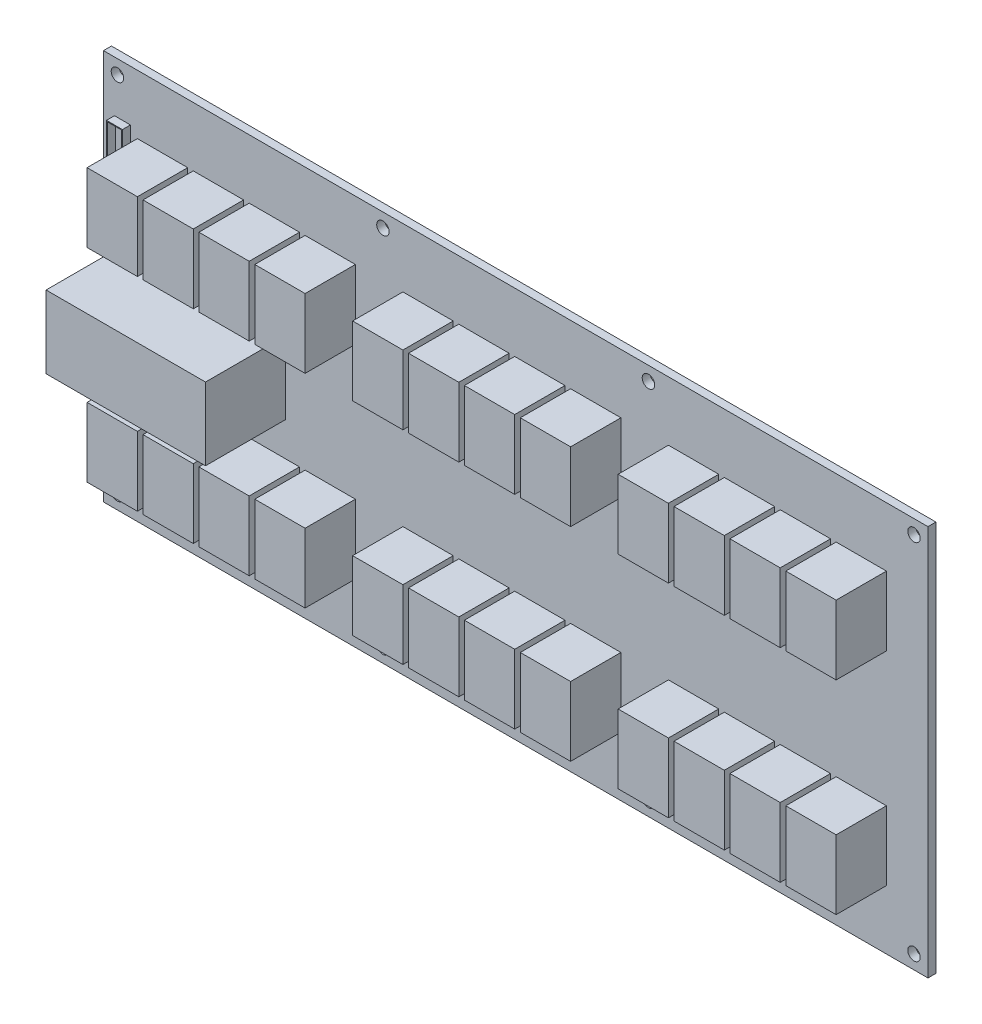
SolidWorks part; units mm, degrees
ref_plane "Front Plane" through (0, 0, 0) normal (0, 0, 1) x (1, 0, 0)
ref_plane "Top Plane" through (0, 0, 0) normal (0, 1, 0) x (1, 0, 0)
ref_plane "Right Plane" through (0, 0, 0) normal (1, 0, 0) x (0, 0, -1)
sketch "Sketch1" plane through (0, 0, 0) normal (0, 0, 1) x (1, 0, 0)
  line L1 (0, 0) -> (262.255, 0)
  line L2 (0, 0) -> (0, 124.333)
  line L3 (0, 124.333) -> (262.255, 124.333)
  line L4 (262.255, 0) -> (262.255, 124.333)
  dimension "D1" = 262.255
  dimension "D2" = 124.333
extrude "Boss-Extrude1" add sketch "Sketch1" along normal blind 2.54
hole_wizard "5/32 (0.15625) Diameter Hole1" positions "Sketch4" profile "Sketch3" hole size "5/32" standard "ANSI Inch" end condition through all
sketch "Sketch4" plane through (0, 0, 2.54) normal (0, 0, 1) x (1, 0, 0)
  line L0 (0, 124.333) -> (0, 0) construction
  line L1 (262.255, 124.333) -> (0, 124.333) construction
  line L2 (0, 0) -> (262.255, 0) construction
  point P0 (4.445, 119.888)
  point P2 (88.9, 119.888)
  point P4 (173.355, 119.888)
  point P6 (257.81, 119.888)
  point P8 (4.445, 4.445)
  point P10 (88.9, 4.445)
  point P12 (173.355, 4.445)
  point P14 (257.81, 4.445)
  dimension "D1" = 4.445
  dimension "D2" = 4.445
  dimension "D3" = 4.445
  dimension "D4" = 84.455
  dimension "D5" = 84.455
  dimension "D6" = 84.455
sketch "Sketch3" plane through (4.445, 119.888, 2.54) normal (1, 0, 0) x (0, -1, 0)
  line L0 (0, 0) -> (0, 2.54)
  line L1 (0, 2.54) -> (1.9844, 2.54)
  line L2 (1.9844, 2.54) -> (1.9844, 0)
  line L5 (1.9844, 0) -> (0, 0)
  line L11 (0, -6.35) -> (0, 107.95) construction
  dimension "Thru Hole Dia." = 3.9688
  dimension "Thru Hole Depth" = 2.54
sketch "Sketch12" plane through (0, 0, 2.54) normal (0, 0, 1) x (1, 0, 0)
  line L1 (3.5048, 108.1512) -> (8.5848, 108.1512)
  line L2 (3.5048, 108.1512) -> (3.5048, 81.2272)
  line L3 (3.5048, 81.2272) -> (8.5848, 81.2272)
  line L4 (8.5848, 108.1512) -> (8.5848, 81.2272)
  line L5 (3.8802, 107.8854) -> (8.2478, 107.8854)
  line L6 (3.8802, 107.8854) -> (3.8802, 81.6126)
  line L7 (3.8802, 81.6126) -> (8.2478, 81.6126)
  line L8 (8.2478, 107.8854) -> (8.2478, 81.6126)
extrude "Boss-Extrude2" add sketch "Sketch12" along normal blind 2.54
sketch "Sketch13" plane through (0, 0, 2.54) normal (0, 0, 1) x (1, 0, 0)
  line L1 (7.1463, 74.6686) -> (57.8568, 74.6686)
  line L2 (7.1463, 74.6686) -> (7.1463, 51.5898)
  line L3 (7.1463, 51.5898) -> (57.8568, 51.5898)
  line L4 (57.8568, 74.6686) -> (57.8568, 51.5898)
extrude "Boss-Extrude3" add sketch "Sketch13" along normal blind 25.4
sketch "Sketch14" plane through (7.1463, 0, 0) normal (-1, 0, 0) x (0, 0, 1)
  line L1 (7.5475, 72.2487) -> (23.276, 72.2487)
  line L2 (7.5475, 72.2487) -> (7.5475, 55.1316)
  line L3 (7.5475, 55.1316) -> (23.276, 55.1316)
  line L4 (23.276, 72.2487) -> (23.276, 55.1316)
extrude "Cut-Extrude1" cut sketch "Sketch14" against normal blind 25.4
sketch "Sketch16" plane through (0, 0, 2.54) normal (0, 0, 1) x (1, 0, 0)
  line L0 (95.25, 105.4897) -> (111.252, 105.4897)
  line L1 (10.795, 105.4897) -> (26.797, 105.4897)
  line L2 (10.795, 105.4897) -> (10.795, 83.4933)
  line L3 (10.795, 83.4933) -> (26.797, 83.4933)
  line L4 (26.797, 105.4897) -> (26.797, 83.4933)
  line L5 (95.25, 105.4897) -> (95.25, 83.4933)
  line L6 (95.25, 83.4933) -> (111.252, 83.4933)
  line L7 (111.252, 105.4897) -> (111.252, 83.4933)
  line L8 (179.705, 105.4897) -> (195.707, 105.4897)
  line L9 (179.705, 105.4897) -> (179.705, 83.4933)
  line L10 (179.705, 83.4933) -> (195.707, 83.4933)
  line L11 (195.707, 105.4897) -> (195.707, 83.4933)
  line L16 (4.445, 119.888) -> (4.445, 4.445) construction
  line L17 (88.9, 119.888) -> (88.9, 4.445) construction
  line L18 (173.355, 119.888) -> (173.355, 4.445) construction
  line L19 (257.81, 119.888) -> (257.81, 4.445) construction
  dimension "D1" = 21.9964
  dimension "D2" = 16.002
  dimension "D3" = 21.9964
  dimension "D4" = 16.002
  dimension "D5" = 21.9964
  dimension "D6" = 16.002
  dimension "D9" = 6.35
  dimension "D10" = 6.35
  dimension "D11" = 6.35
extrude "Boss-Extrude5" add sketch "Sketch16" along normal blind 16.002
pattern_linear "LPattern1" count 4 spacing 17.78 along (1, 0, 0) of "Boss-Extrude5"
ref_plane "Plane1" through (0, 62.1665, 0) normal (0, 1, 0) x (1, 0, 0)
mirror "Mirror1" about plane through (0, 62.1665, 0) normal (0, 1, 0) of "LPattern1", "Boss-Extrude5"
